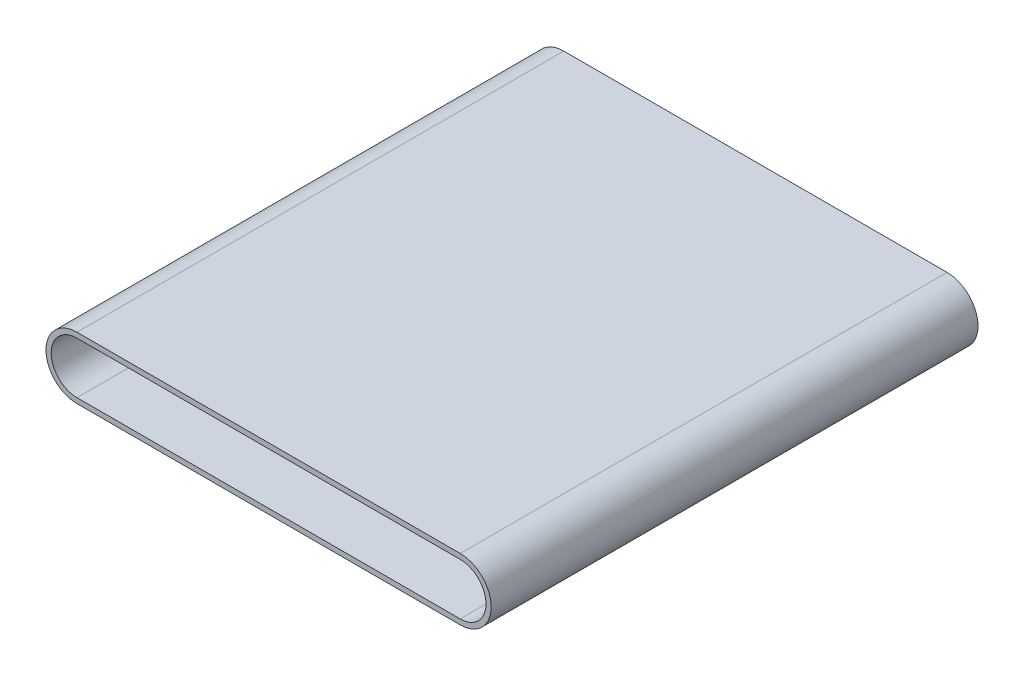
SolidWorks part; units mm, degrees
ref_plane "Front Plane" through (0, 0, 0) normal (0, 0, 1) x (1, 0, 0)
ref_plane "Top Plane" through (0, 0, 0) normal (0, 1, 0) x (1, 0, 0)
ref_plane "Right Plane" through (0, 0, 0) normal (1, 0, 0) x (0, 0, -1)
sketch "Sketch2" plane through (0, 0, 0) normal (0, 0, 1) x (1, 0, 0)
  line L0 (0, 0) -> (1, 0) construction
  line L1 (0, 0) -> (0, 1) construction
  line L2 (0, -24.875) -> (-370, -24.875)
  line L3 (-370, 24.875) -> (0, 24.875)
  arc A0 (0, 24.875) -> (0, -24.875) centre (0, 0) cw
  arc A1 (-370, -24.875) -> (-370, 24.875) centre (-370, 0) cw
sketch "Sketch3" plane through (0, 0, 0) normal (1, 0, 0) x (0, 0, -1)
  line L0 (0, 24.875) -> (0, -24.875) construction
  line L1 (-235, 24.875) -> (235, 24.875)
  line L2 (-235, 24.875) -> (-235, 29.875)
  line L3 (-235, 29.875) -> (235, 29.875)
  line L4 (235, 24.875) -> (235, 29.875)
  dimension "D1" = 235
  dimension "D2" = 235
  dimension "D3" = 5
  dimension "D4" = 24.875
sweep "Sweep2" add profiles "Sketch3" path "Sketch2"
